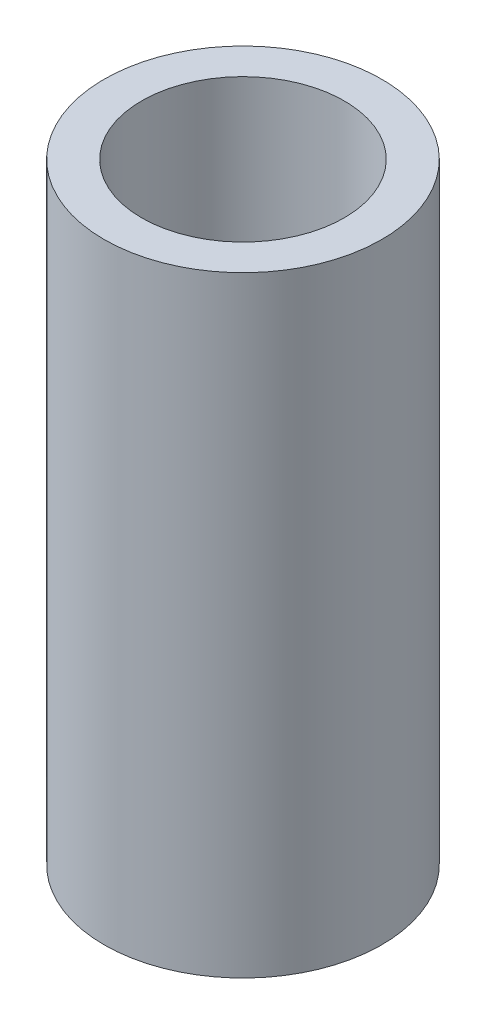
SolidWorks part; units mm, degrees
ref_plane "Спереди" through (0, 0, 0) normal (0, 0, 1) x (1, 0, 0)
ref_plane "Сверху" through (0, 0, 0) normal (0, 1, 0) x (1, 0, 0)
ref_plane "Справа" through (0, 0, 0) normal (1, 0, 0) x (0, 0, -1)
sketch "Эскиз1" plane through (0, 0, 0) normal (0, 1, 0) x (1, 0, 0)
  circle A0 centre (0, 0) radius 3.65
  circle A1 centre (0, 0) radius 5
  dimension "D1" = 10
  dimension "D2" = 7.3
extrude "Бобышка-Вытянуть1" add sketch "Эскиз1" along normal blind 22
